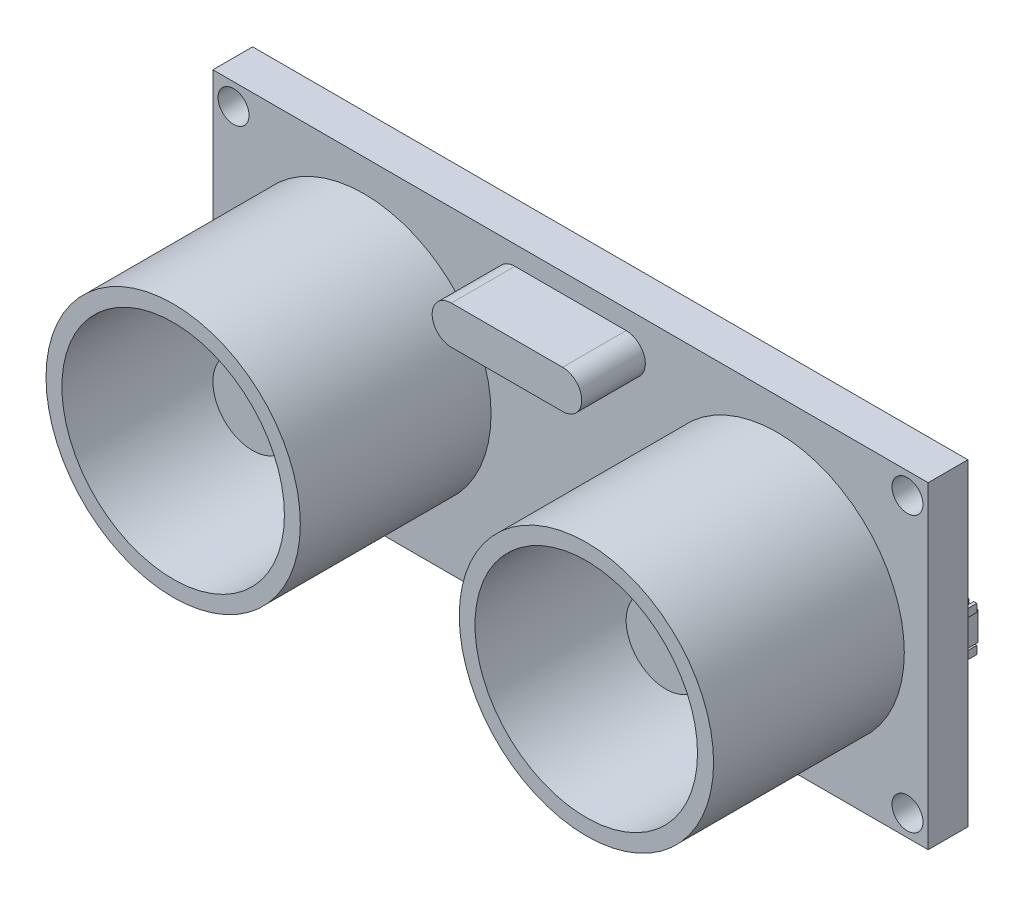
SolidWorks part; units mm, degrees
ref_plane "Front Plane" through (0, 0, 0) normal (0, 0, 1) x (1, 0, 0)
ref_plane "Top Plane" through (0, 0, 0) normal (0, 1, 0) x (1, 0, 0)
ref_plane "Right Plane" through (0, 0, 0) normal (1, 0, 0) x (0, 0, -1)
sketch "Sketch1" plane through (0, 0, 0) normal (0, 0, 1) x (1, 0, 0)
  line L1 (-22.5, 10) -> (22.5, 10)
  line L2 (-22.5, 10) -> (-22.5, -10)
  line L3 (-22.5, -10) -> (22.5, -10)
  line L4 (22.5, 10) -> (22.5, -10)
  line L5 (-22.5, 10) -> (22.5, -10) construction
  line L6 (-22.5, -10) -> (22.5, 10) construction
  point P0 (0, 0)
  dimension "D1" = 45
  dimension "D2" = 20
extrude "Boss-Extrude1" add sketch "Sketch1" along normal blind 2.5
sketch "Sketch2" plane through (0, 0, 2.5) normal (0, 0, 1) x (1, 0, 0)
  line L0 (22.5, 10) -> (-22.5, 10) construction
  line L2 (-22.5, 10) -> (-22.5, -10) construction
  line L3 (22.5, -10) -> (22.5, 10) construction
  circle A0 centre (-13, 0) radius 8
  circle A1 centre (13, 0) radius 8
  dimension "D1" = 16
  dimension "D2" = 16
  dimension "D3" = 9.5
  dimension "D4" = 9.5
  dimension "D5" = 10
extrude "Boss-Extrude2" add sketch "Sketch2" along normal blind 12
sketch "Sketch3" plane through (0, 0, 14.5) normal (0, 0, 1) x (1, 0, 0)
  circle A0 centre (-13, -0.01) radius 7
  circle A1 centre (12.99, 0) radius 7
  circle A2 centre (13, 0) radius 8 construction
  circle A3 centre (-13, 0) radius 8 construction
  dimension "D1" = 14
  dimension "D2" = 14
  dimension "D3" = 0.01
  dimension "D4" = 0.01
extrude "Cut-Extrude2" cut sketch "Sketch3" against normal blind 12 contours A1 | A0
sketch "Sketch5" plane through (0, 0, 2.5) normal (0, 0, 1) x (1, 0, 0)
  circle A0 centre (-13, 0) radius 4
  circle A1 centre (13, 0) radius 4
  dimension "D1" = 8
  dimension "D2" = 8
extrude "Boss-Extrude3" add sketch "Sketch5" along normal blind 5
sketch "Sketch6" plane through (0, 0, 7.5) normal (0, 0, 1) x (1, 0, 0)
  circle A0 centre (-13, 0) radius 2.5
  circle A1 centre (13, 0) radius 2.5
  dimension "D1" = 5
  dimension "D2" = 5
extrude "Boss-Extrude4" add sketch "Sketch6" along normal blind 2
sketch "Sketch7" plane through (0, 0, 2.5) normal (0, 0, 1) x (1, 0, 0)
  line L0 (-22.5, 10) -> (-22.5, -10) construction
  line L1 (22.5, 10) -> (-22.5, 10) construction
  line L2 (-22.5, -10) -> (22.5, -10) construction
  line L3 (22.5, -10) -> (22.5, 10) construction
  circle A0 centre (-21.2, 8.65) radius 0.975
  circle A1 centre (-21.2, -8.65) radius 0.975
  circle A2 centre (21.2, -8.65) radius 0.975
  circle A3 centre (21.2, 8.65) radius 0.975
  dimension "D1" = 1.3
  dimension "D9" = 1.95
  dimension "D10" = 1.95
  dimension "D11" = 1.95
  dimension "D12" = 1.95
  dimension "D2" = 1.35
  dimension "D3" = 1.3
  dimension "D4" = 1.35
  dimension "D5" = 1.35
  dimension "D6" = 1.3
  dimension "D7" = 1.3
  dimension "D8" = 1.35
  dimension "D13" = 17.3
  dimension "D14" = 42.4
  dimension "D15" = 42.4
  dimension "D16" = 17.3
extrude "Cut-Extrude4" cut sketch "Sketch7" against normal blind 12
sketch "Sketch8" plane through (0, 0, 2.5) normal (0, 0, 1) x (1, 0, 0)
  line L0 (-3.5, 7.585) -> (3.5, 7.585) construction
  line L1 (-3.5, 8.79) -> (3.5, 8.79)
  line L2 (-3.5, 6.38) -> (3.5, 6.38)
  line L3 (-22.5, 10) -> (-22.5, -10) construction
  line L4 (22.5, -10) -> (22.5, 10) construction
  line L5 (22.5, 10) -> (-22.5, 10) construction
  arc A0 (-3.5, 8.79) -> (-3.5, 6.38) centre (-3.5, 7.585) ccw
  arc A1 (3.5, 6.38) -> (3.5, 8.79) centre (3.5, 7.585) ccw
  point P2 (0, 7.585)
  dimension "D1" = 19
  dimension "D2" = 19
  dimension "D5" = 7
  dimension "D6" = 2.41
  dimension "D7" = 1.21
extrude "Boss-Extrude5" add sketch "Sketch8" along normal blind 4
sketch "Sketch9" plane through (0, 0, 0) normal (0, 0, -1) x (-1, 0, 0)
  line L1 (-22.136, 1.1575) -> (-17.0213, 1.1575)
  line L2 (-22.136, 1.1575) -> (-22.136, -0.6364)
  line L3 (-22.136, -0.6364) -> (-17.0213, -0.6364)
  line L4 (-17.0213, 1.1575) -> (-17.0213, -0.6364)
  line L5 (-22.136, 1.1575) -> (-17.0213, -0.6364) construction
  line L6 (-22.136, -0.6364) -> (-17.0213, 1.1575) construction
  point P0 (-19.5787, 0.2606)
extrude "Boss-Extrude6" add sketch "Sketch9" along normal blind 1
sketch "Sketch10" plane through (0, 0, 0) normal (0, 0, -1) x (-1, 0, 0)
  line L1 (-2.8938, 0.9646) -> (2.8938, 0.9646)
  line L2 (-2.8938, 0.9646) -> (-2.8938, -0.9646)
  line L3 (-2.8938, -0.9646) -> (2.8938, -0.9646)
  line L4 (2.8938, 0.9646) -> (2.8938, -0.9646)
  line L5 (-2.8938, 0.9646) -> (2.8938, -0.9646) construction
  line L6 (-2.8938, -0.9646) -> (2.8938, 0.9646) construction
  line L7 (19.4136, 2.315) -> (21.5357, 2.315)
  line L8 (19.4136, 2.315) -> (19.4136, -2.315)
  line L9 (19.4136, -2.315) -> (21.5357, -2.315)
  line L10 (21.5357, 2.315) -> (21.5357, -2.315)
  line L11 (19.4136, 2.315) -> (21.5357, -2.315) construction
  line L12 (19.4136, -2.315) -> (21.5357, 2.315) construction
  point P0 (0, 0)
  point P6 (20.4746, 0)
extrude "Boss-Extrude7" add sketch "Sketch10" along normal blind 1
sketch "Sketch12" plane through (0, 0, 0) normal (0, 0, -1) x (-1, 0, 0)
  circle A0 centre (-15.4898, 5.0275) radius 1
  circle A1 centre (-15.4898, -5.3069) radius 1
  circle A2 centre (13.7773, -5.3069) radius 1
  circle A3 centre (13.7773, 5.0275) radius 1
  dimension "D1" = 2
  dimension "D2" = 2
  dimension "D3" = 2
  dimension "D4" = 2
extrude "Boss-Extrude8" add sketch "Sketch12" along normal blind 0.5 draft 62
sketch "Sketch13" plane through (0, 0, 0) normal (0, 0, -1) x (-1, 0, 0)
  circle A0 centre (-3.3278, 7.138) radius 0.5
  circle A1 centre (3.9548, 7.138) radius 0.5
  dimension "D1" = 1
  dimension "D2" = 1
extrude "Boss-Extrude9" add sketch "Sketch13" along normal blind 0.5 draft 45
ref_plane "Plane1" through (0, 0, -0.8) normal (0, 0, 1) x (1, 0, 0)
sketch "Sketch15" plane through (0, 0, -0.8) normal (0, 0, 1) x (1, 0, 0)
  line L0 (17.0213, 1.1575) -> (22.136, 1.1575) construction
  line L1 (22.2579, 1.6575) -> (22.0579, 1.6575)
  line L2 (22.2579, 1.6575) -> (22.2579, 1.1575)
  line L3 (22.2579, 1.1575) -> (22.0579, 1.1575)
  line L4 (22.0579, 1.6575) -> (22.0579, 1.1575)
  line L5 (22.2579, 1.6575) -> (22.0579, 1.1575) construction
  line L6 (22.2579, 1.1575) -> (22.0579, 1.6575) construction
  line L7 (21.5579, 1.6575) -> (21.5579, 1.1575)
  line L8 (22.2579, -0.6364) -> (22.0579, -0.6364)
  line L9 (22.2579, -0.6364) -> (22.2579, -1.1364)
  line L10 (22.2579, -1.1364) -> (22.0579, -1.1364)
  line L11 (22.0579, -0.6364) -> (22.0579, -1.1364)
  line L12 (22.2579, -0.6364) -> (22.0579, -1.1364) construction
  line L13 (22.2579, -1.1364) -> (22.0579, -0.6364) construction
  line L14 (22.136, -0.6364) -> (17.0213, -0.6364) construction
  line L15 (21.7579, 1.6575) -> (21.5579, 1.6575)
  line L16 (21.7579, 1.6575) -> (21.7579, 1.1575)
  line L17 (21.7579, 1.1575) -> (21.5579, 1.1575)
  line L18 (21.7579, -0.6364) -> (21.5579, -0.6364)
  line L19 (21.5579, -0.6364) -> (21.5579, -1.1364)
  line L20 (21.7579, -1.1364) -> (21.5579, -1.1364)
  line L21 (21.7579, -0.6364) -> (21.7579, -1.1364)
  line L22 (21.0579, 1.6575) -> (21.0579, 1.1575)
  line L23 (21.2579, 1.6575) -> (21.0579, 1.6575)
  line L24 (21.2579, 1.6575) -> (21.2579, 1.1575)
  line L25 (21.2579, 1.1575) -> (21.0579, 1.1575)
  line L26 (21.2579, -0.6364) -> (21.0579, -0.6364)
  line L27 (21.0579, -0.6364) -> (21.0579, -1.1364)
  line L28 (21.2579, -1.1364) -> (21.0579, -1.1364)
  line L29 (21.2579, -0.6364) -> (21.2579, -1.1364)
  line L30 (20.5579, 1.6575) -> (20.5579, 1.1575)
  line L31 (20.7579, 1.6575) -> (20.5579, 1.6575)
  line L32 (20.7579, 1.6575) -> (20.7579, 1.1575)
  line L33 (20.7579, 1.1575) -> (20.5579, 1.1575)
  line L34 (20.7579, -0.6364) -> (20.5579, -0.6364)
  line L35 (20.5579, -0.6364) -> (20.5579, -1.1364)
  line L36 (20.7579, -1.1364) -> (20.5579, -1.1364)
  line L37 (20.7579, -0.6364) -> (20.7579, -1.1364)
  line L38 (20.0579, 1.6575) -> (20.0579, 1.1575)
  line L39 (20.2579, 1.6575) -> (20.0579, 1.6575)
  line L40 (20.2579, 1.6575) -> (20.2579, 1.1575)
  line L41 (20.2579, 1.1575) -> (20.0579, 1.1575)
  line L42 (20.2579, -0.6364) -> (20.0579, -0.6364)
  line L43 (20.0579, -0.6364) -> (20.0579, -1.1364)
  line L44 (20.2579, -1.1364) -> (20.0579, -1.1364)
  line L45 (20.2579, -0.6364) -> (20.2579, -1.1364)
  line L46 (19.5579, 1.6575) -> (19.5579, 1.1575)
  line L47 (19.7579, 1.6575) -> (19.5579, 1.6575)
  line L48 (19.7579, 1.6575) -> (19.7579, 1.1575)
  line L49 (19.7579, 1.1575) -> (19.5579, 1.1575)
  line L50 (19.7579, -0.6364) -> (19.5579, -0.6364)
  line L51 (19.5579, -0.6364) -> (19.5579, -1.1364)
  line L52 (19.7579, -1.1364) -> (19.5579, -1.1364)
  line L53 (19.7579, -0.6364) -> (19.7579, -1.1364)
  line L54 (19.0579, 1.6575) -> (19.0579, 1.1575)
  line L55 (19.2579, 1.6575) -> (19.0579, 1.6575)
  line L56 (19.2579, 1.6575) -> (19.2579, 1.1575)
  line L57 (19.2579, 1.1575) -> (19.0579, 1.1575)
  line L58 (19.2579, -0.6364) -> (19.0579, -0.6364)
  line L59 (19.0579, -0.6364) -> (19.0579, -1.1364)
  line L60 (19.2579, -1.1364) -> (19.0579, -1.1364)
  line L61 (19.2579, -0.6364) -> (19.2579, -1.1364)
  line L62 (18.5579, 1.6575) -> (18.5579, 1.1575)
  line L63 (18.7579, 1.6575) -> (18.5579, 1.6575)
  line L64 (18.7579, 1.6575) -> (18.7579, 1.1575)
  line L65 (18.7579, 1.1575) -> (18.5579, 1.1575)
  line L66 (18.7579, -0.6364) -> (18.5579, -0.6364)
  line L67 (18.5579, -0.6364) -> (18.5579, -1.1364)
  line L68 (18.7579, -1.1364) -> (18.5579, -1.1364)
  line L69 (18.7579, -0.6364) -> (18.7579, -1.1364)
  line L70 (18.0579, 1.6575) -> (18.0579, 1.1575)
  line L71 (18.2579, 1.6575) -> (18.0579, 1.6575)
  line L72 (18.2579, 1.6575) -> (18.2579, 1.1575)
  line L73 (18.2579, 1.1575) -> (18.0579, 1.1575)
  line L74 (18.2579, -0.6364) -> (18.0579, -0.6364)
  line L75 (18.0579, -0.6364) -> (18.0579, -1.1364)
  line L76 (18.2579, -1.1364) -> (18.0579, -1.1364)
  line L77 (18.2579, -0.6364) -> (18.2579, -1.1364)
  line L78 (17.5579, 1.6575) -> (17.5579, 1.1575)
  line L79 (17.7579, 1.6575) -> (17.5579, 1.6575)
  line L80 (17.7579, 1.6575) -> (17.7579, 1.1575)
  line L81 (17.7579, 1.1575) -> (17.5579, 1.1575)
  line L82 (17.7579, -0.6364) -> (17.5579, -0.6364)
  line L83 (17.5579, -0.6364) -> (17.5579, -1.1364)
  line L84 (17.7579, -1.1364) -> (17.5579, -1.1364)
  line L85 (17.7579, -0.6364) -> (17.7579, -1.1364)
  line L86 (22.0579, 1.6575) -> (21.5579, 1.6575) construction
  point P0 (22.1579, 1.4075)
  point P7 (22.1579, -0.8864)
  dimension "D1" = 0.5
  dimension "D2" = 0.2
  dimension "D3" = 0.2
  dimension "D4" = 0.5
  dimension "D5" = 10
  dimension "D6" = 0.5
extrude "Boss-Extrude10" add sketch "Sketch15" along normal up to surface (0.8 mm away) up to face at (-3.4548, 7.138, 0)
sketch "Sketch16" plane through (0, 0, -0.8) normal (0, 0, 1) x (1, 0, 0)
  line L0 (-2.8938, 0.9646) -> (2.8938, 0.9646) construction
  line L1 (2.7664, 1.4646) -> (2.5664, 1.4646)
  line L2 (2.7664, 1.4646) -> (2.7664, 0.9646)
  line L3 (2.7664, 0.9646) -> (2.5664, 0.9646)
  line L4 (2.5664, 1.4646) -> (2.5664, 0.9646)
  line L5 (2.7664, 1.4646) -> (2.5664, 0.9646) construction
  line L6 (2.7664, 0.9646) -> (2.5664, 1.4646) construction
  line L7 (2.2664, 1.4646) -> (2.0664, 1.4646)
  line L8 (2.7664, -0.9646) -> (2.5664, -0.9646)
  line L9 (2.7664, -0.9646) -> (2.7664, -1.4646)
  line L10 (2.7664, -1.4646) -> (2.5664, -1.4646)
  line L11 (2.5664, -0.9646) -> (2.5664, -1.4646)
  line L12 (2.7664, -0.9646) -> (2.5664, -1.4646) construction
  line L13 (2.7664, -1.4646) -> (2.5664, -0.9646) construction
  line L14 (-2.8938, 0.9646) -> (2.8938, 0.9646) construction
  line L15 (2.8938, -0.9646) -> (-2.8938, -0.9646) construction
  line L16 (2.0664, 1.4646) -> (2.0664, 0.9646)
  line L17 (2.2664, 0.9646) -> (2.0664, 0.9646)
  line L18 (2.2664, 1.4646) -> (2.2664, 0.9646)
  line L19 (2.2664, -1.4646) -> (2.0664, -1.4646)
  line L20 (2.2664, -0.9646) -> (2.2664, -1.4646)
  line L21 (2.2664, -0.9646) -> (2.0664, -0.9646)
  line L22 (2.0664, -0.9646) -> (2.0664, -1.4646)
  line L23 (1.7664, 1.4646) -> (1.5664, 1.4646)
  line L24 (1.5664, 1.4646) -> (1.5664, 0.9646)
  line L25 (1.7664, 0.9646) -> (1.5664, 0.9646)
  line L26 (1.7664, 1.4646) -> (1.7664, 0.9646)
  line L27 (1.7664, -1.4646) -> (1.5664, -1.4646)
  line L28 (1.7664, -0.9646) -> (1.7664, -1.4646)
  line L29 (1.7664, -0.9646) -> (1.5664, -0.9646)
  line L30 (1.5664, -0.9646) -> (1.5664, -1.4646)
  line L31 (1.2664, 1.4646) -> (1.0664, 1.4646)
  line L32 (1.0664, 1.4646) -> (1.0664, 0.9646)
  line L33 (1.2664, 0.9646) -> (1.0664, 0.9646)
  line L34 (1.2664, 1.4646) -> (1.2664, 0.9646)
  line L35 (1.2664, -1.4646) -> (1.0664, -1.4646)
  line L36 (1.2664, -0.9646) -> (1.2664, -1.4646)
  line L37 (1.2664, -0.9646) -> (1.0664, -0.9646)
  line L38 (1.0664, -0.9646) -> (1.0664, -1.4646)
  line L39 (0.7664, 1.4646) -> (0.5664, 1.4646)
  line L40 (0.5664, 1.4646) -> (0.5664, 0.9646)
  line L41 (0.7664, 0.9646) -> (0.5664, 0.9646)
  line L42 (0.7664, 1.4646) -> (0.7664, 0.9646)
  line L43 (0.7664, -1.4646) -> (0.5664, -1.4646)
  line L44 (0.7664, -0.9646) -> (0.7664, -1.4646)
  line L45 (0.7664, -0.9646) -> (0.5664, -0.9646)
  line L46 (0.5664, -0.9646) -> (0.5664, -1.4646)
  line L47 (0.2664, 1.4646) -> (0.0664, 1.4646)
  line L48 (0.0664, 1.4646) -> (0.0664, 0.9646)
  line L49 (0.2664, 0.9646) -> (0.0664, 0.9646)
  line L50 (0.2664, 1.4646) -> (0.2664, 0.9646)
  line L51 (0.2664, -1.4646) -> (0.0664, -1.4646)
  line L52 (0.2664, -0.9646) -> (0.2664, -1.4646)
  line L53 (0.2664, -0.9646) -> (0.0664, -0.9646)
  line L54 (0.0664, -0.9646) -> (0.0664, -1.4646)
  line L55 (-0.2336, 1.4646) -> (-0.4336, 1.4646)
  line L56 (-0.4336, 1.4646) -> (-0.4336, 0.9646)
  line L57 (-0.2336, 0.9646) -> (-0.4336, 0.9646)
  line L58 (-0.2336, 1.4646) -> (-0.2336, 0.9646)
  line L59 (-0.2336, -1.4646) -> (-0.4336, -1.4646)
  line L60 (-0.2336, -0.9646) -> (-0.2336, -1.4646)
  line L61 (-0.2336, -0.9646) -> (-0.4336, -0.9646)
  line L62 (-0.4336, -0.9646) -> (-0.4336, -1.4646)
  line L63 (-0.7336, 1.4646) -> (-0.9336, 1.4646)
  line L64 (-0.9336, 1.4646) -> (-0.9336, 0.9646)
  line L65 (-0.7336, 0.9646) -> (-0.9336, 0.9646)
  line L66 (-0.7336, 1.4646) -> (-0.7336, 0.9646)
  line L67 (-0.7336, -1.4646) -> (-0.9336, -1.4646)
  line L68 (-0.7336, -0.9646) -> (-0.7336, -1.4646)
  line L69 (-0.7336, -0.9646) -> (-0.9336, -0.9646)
  line L70 (-0.9336, -0.9646) -> (-0.9336, -1.4646)
  line L71 (-1.2336, 1.4646) -> (-1.4336, 1.4646)
  line L72 (-1.4336, 1.4646) -> (-1.4336, 0.9646)
  line L73 (-1.2336, 0.9646) -> (-1.4336, 0.9646)
  line L74 (-1.2336, 1.4646) -> (-1.2336, 0.9646)
  line L75 (-1.2336, -1.4646) -> (-1.4336, -1.4646)
  line L76 (-1.2336, -0.9646) -> (-1.2336, -1.4646)
  line L77 (-1.2336, -0.9646) -> (-1.4336, -0.9646)
  line L78 (-1.4336, -0.9646) -> (-1.4336, -1.4646)
  line L79 (-1.7336, 1.4646) -> (-1.9336, 1.4646)
  line L80 (-1.9336, 1.4646) -> (-1.9336, 0.9646)
  line L81 (-1.7336, 0.9646) -> (-1.9336, 0.9646)
  line L82 (-1.7336, 1.4646) -> (-1.7336, 0.9646)
  line L83 (-1.7336, -1.4646) -> (-1.9336, -1.4646)
  line L84 (-1.7336, -0.9646) -> (-1.7336, -1.4646)
  line L85 (-1.7336, -0.9646) -> (-1.9336, -0.9646)
  line L86 (-1.9336, -0.9646) -> (-1.9336, -1.4646)
  line L87 (-2.2336, 1.4646) -> (-2.4336, 1.4646)
  line L88 (-2.4336, 1.4646) -> (-2.4336, 0.9646)
  line L89 (-2.2336, 0.9646) -> (-2.4336, 0.9646)
  line L90 (-2.2336, 1.4646) -> (-2.2336, 0.9646)
  line L91 (-2.2336, -1.4646) -> (-2.4336, -1.4646)
  line L92 (-2.2336, -0.9646) -> (-2.2336, -1.4646)
  line L93 (-2.2336, -0.9646) -> (-2.4336, -0.9646)
  line L94 (-2.4336, -0.9646) -> (-2.4336, -1.4646)
  line L95 (2.7664, 1.4646) -> (2.2664, 1.4646) construction
  point P0 (2.6664, 1.2146)
  point P7 (2.6664, -1.2146)
  dimension "D1" = 0.5
  dimension "D2" = 0.2
  dimension "D3" = 0.5
  dimension "D4" = 0.2
  dimension "D6" = 0.5
  dimension "D5" = 11
extrude "Boss-Extrude11" add sketch "Sketch16" along normal up to surface (0.8 mm away) up to face at (-3.4548, 7.138, 0)
sketch "Sketch17" plane through (0, 0, -0.8) normal (0, 0, 1) x (1, 0, 0)
  line L0 (-19.4136, 2.1119) -> (-21.5357, 2.1119) construction
  line L1 (-21.5357, 2.1119) -> (-22.079, 2.1119)
  line L2 (-21.5357, 2.1119) -> (-21.5357, 1.9119)
  line L3 (-21.5357, 1.9119) -> (-22.079, 1.9119)
  line L4 (-22.079, 2.1119) -> (-22.079, 1.9119)
  line L5 (-21.5357, 2.1119) -> (-22.079, 1.9119) construction
  line L6 (-21.5357, 1.9119) -> (-22.079, 2.1119) construction
  line L7 (-18.9136, 2.1119) -> (-19.4136, 2.1119)
  line L8 (-18.9136, 2.1119) -> (-18.9136, 1.9119)
  line L9 (-18.9136, 1.9119) -> (-19.4136, 1.9119)
  line L10 (-19.4136, 2.1119) -> (-19.4136, 1.9119)
  line L11 (-18.9136, 2.1119) -> (-19.4136, 1.9119) construction
  line L12 (-18.9136, 1.9119) -> (-19.4136, 2.1119) construction
  line L13 (-19.4136, 2.315) -> (-19.4136, -2.315) construction
  line L14 (-21.5357, -2.315) -> (-21.5357, 2.315) construction
  line L15 (-18.9136, 1.6119) -> (-19.4136, 1.6119)
  line L16 (-18.9136, 1.6119) -> (-18.9136, 1.4119)
  line L17 (-18.9136, 1.4119) -> (-19.4136, 1.4119)
  line L18 (-19.4136, 1.6119) -> (-19.4136, 1.4119)
  line L19 (-21.5357, 1.6119) -> (-22.079, 1.6119)
  line L20 (-21.5357, 1.6119) -> (-21.5357, 1.4119)
  line L21 (-21.5357, 1.4119) -> (-22.079, 1.4119)
  line L22 (-22.079, 1.6119) -> (-22.079, 1.4119)
  line L23 (-18.9136, 1.1119) -> (-19.4136, 1.1119)
  line L24 (-18.9136, 1.1119) -> (-18.9136, 0.9119)
  line L25 (-18.9136, 0.9119) -> (-19.4136, 0.9119)
  line L26 (-19.4136, 1.1119) -> (-19.4136, 0.9119)
  line L27 (-21.5357, 1.1119) -> (-22.079, 1.1119)
  line L28 (-21.5357, 1.1119) -> (-21.5357, 0.9119)
  line L29 (-21.5357, 0.9119) -> (-22.079, 0.9119)
  line L30 (-22.079, 1.1119) -> (-22.079, 0.9119)
  line L31 (-18.9136, 0.6119) -> (-19.4136, 0.6119)
  line L32 (-18.9136, 0.6119) -> (-18.9136, 0.4119)
  line L33 (-18.9136, 0.4119) -> (-19.4136, 0.4119)
  line L34 (-19.4136, 0.6119) -> (-19.4136, 0.4119)
  line L35 (-21.5357, 0.6119) -> (-22.079, 0.6119)
  line L36 (-21.5357, 0.6119) -> (-21.5357, 0.4119)
  line L37 (-21.5357, 0.4119) -> (-22.079, 0.4119)
  line L38 (-22.079, 0.6119) -> (-22.079, 0.4119)
  line L39 (-18.9136, 0.1119) -> (-19.4136, 0.1119)
  line L40 (-18.9136, 0.1119) -> (-18.9136, -0.0881)
  line L41 (-18.9136, -0.0881) -> (-19.4136, -0.0881)
  line L42 (-19.4136, 0.1119) -> (-19.4136, -0.0881)
  line L43 (-21.5357, 0.1119) -> (-22.079, 0.1119)
  line L44 (-21.5357, 0.1119) -> (-21.5357, -0.0881)
  line L45 (-21.5357, -0.0881) -> (-22.079, -0.0881)
  line L46 (-22.079, 0.1119) -> (-22.079, -0.0881)
  line L47 (-18.9136, -0.3881) -> (-19.4136, -0.3881)
  line L48 (-18.9136, -0.3881) -> (-18.9136, -0.5881)
  line L49 (-18.9136, -0.5881) -> (-19.4136, -0.5881)
  line L50 (-19.4136, -0.3881) -> (-19.4136, -0.5881)
  line L51 (-21.5357, -0.3881) -> (-22.079, -0.3881)
  line L52 (-21.5357, -0.3881) -> (-21.5357, -0.5881)
  line L53 (-21.5357, -0.5881) -> (-22.079, -0.5881)
  line L54 (-22.079, -0.3881) -> (-22.079, -0.5881)
  line L55 (-18.9136, -0.8881) -> (-19.4136, -0.8881)
  line L56 (-18.9136, -0.8881) -> (-18.9136, -1.0881)
  line L57 (-18.9136, -1.0881) -> (-19.4136, -1.0881)
  line L58 (-19.4136, -0.8881) -> (-19.4136, -1.0881)
  line L59 (-21.5357, -0.8881) -> (-22.079, -0.8881)
  line L60 (-21.5357, -0.8881) -> (-21.5357, -1.0881)
  line L61 (-21.5357, -1.0881) -> (-22.079, -1.0881)
  line L62 (-22.079, -0.8881) -> (-22.079, -1.0881)
  line L63 (-18.9136, -1.3881) -> (-19.4136, -1.3881)
  line L64 (-18.9136, -1.3881) -> (-18.9136, -1.5881)
  line L65 (-18.9136, -1.5881) -> (-19.4136, -1.5881)
  line L66 (-19.4136, -1.3881) -> (-19.4136, -1.5881)
  line L67 (-21.5357, -1.3881) -> (-22.079, -1.3881)
  line L68 (-21.5357, -1.3881) -> (-21.5357, -1.5881)
  line L69 (-21.5357, -1.5881) -> (-22.079, -1.5881)
  line L70 (-22.079, -1.3881) -> (-22.079, -1.5881)
  line L71 (-18.9136, -1.8881) -> (-19.4136, -1.8881)
  line L72 (-18.9136, -1.8881) -> (-18.9136, -2.0881)
  line L73 (-18.9136, -2.0881) -> (-19.4136, -2.0881)
  line L74 (-19.4136, -1.8881) -> (-19.4136, -2.0881)
  line L75 (-21.5357, -1.8881) -> (-22.079, -1.8881)
  line L76 (-21.5357, -1.8881) -> (-21.5357, -2.0881)
  line L77 (-21.5357, -2.0881) -> (-22.079, -2.0881)
  line L78 (-22.079, -1.8881) -> (-22.079, -2.0881)
  point P0 (-21.8074, 2.0119)
  point P5 (-19.1636, 2.0119)
  dimension "D1" = 0.2
  dimension "D2" = 0.5
  dimension "D3" = 0.5433
  dimension "D4" = 0.2
  dimension "D5" = 9
extrude "Boss-Extrude12" add sketch "Sketch17" along normal up to surface (0.8 mm away) up to face at (-3.4548, 7.138, 0)
sketch "Sketch18" plane through (0, 0, 0) normal (0, 0, -1) x (-1, 0, 0)
  line L1 (-4.5, -7.199) -> (4.5, -7.199)
  line L2 (-4.5, -7.199) -> (-4.5, -9.199)
  line L3 (-4.5, -9.199) -> (4.5, -9.199)
  line L4 (4.5, -7.199) -> (4.5, -9.199)
  line L5 (-4.5, -7.199) -> (4.5, -9.199) construction
  line L6 (-4.5, -9.199) -> (4.5, -7.199) construction
  line L8 (-22.5, -10) -> (-22.5, 10) construction
  line L9 (22.5, 10) -> (22.5, -10) construction
  point P0 (0, -8.199)
  dimension "D1" = 18
  dimension "D2" = 18
  dimension "D3" = 2
extrude "Boss-Extrude14" add sketch "Sketch18" along normal blind 3 contours L3 L4 L1 L2
sketch "Sketch19" plane through (0, 0, -3) normal (0, 0, -1) x (-1, 0, 0)
  line L1 (-3.858, -7.956) -> (-3.358, -7.956)
  line L2 (-3.858, -7.956) -> (-3.858, -8.456)
  line L3 (-3.858, -8.456) -> (-3.358, -8.456)
  line L4 (-3.358, -7.956) -> (-3.358, -8.456)
  line L5 (-3.858, -7.956) -> (-3.358, -8.456) construction
  line L6 (-3.858, -8.456) -> (-3.358, -7.956) construction
  line L7 (-4.5, -9.199) -> (4.5, -9.199) construction
  line L8 (-4.5, -7.199) -> (4.5, -7.199) construction
  line L9 (-0.858, -7.956) -> (-0.858, -8.456)
  line L10 (-1.358, -7.956) -> (-1.358, -8.456)
  line L11 (-1.358, -7.956) -> (-0.858, -7.956)
  line L12 (-1.358, -8.456) -> (-0.858, -8.456)
  line L13 (1.642, -7.956) -> (1.642, -8.456)
  line L14 (1.142, -7.956) -> (1.142, -8.456)
  line L15 (1.142, -7.956) -> (1.642, -7.956)
  line L16 (1.142, -8.456) -> (1.642, -8.456)
  line L17 (4.142, -7.956) -> (4.142, -8.456)
  line L18 (3.642, -7.956) -> (3.642, -8.456)
  line L19 (3.642, -7.956) -> (4.142, -7.956)
  line L20 (3.642, -8.456) -> (4.142, -8.456)
  point P0 (-3.608, -8.206)
  dimension "D1" = 0.5
  dimension "D2" = 0.5
  dimension "D3" = 0.993
  dimension "D4" = 1.007
  dimension "D5" = 4
extrude "Boss-Extrude15" add sketch "Sketch19" along normal blind 1
sketch "Sketch20" plane through (0, -8.456, 0) normal (0, -1, 0) x (1, 0, 0)
  line L0 (3.858, -4) -> (3.858, -3) construction
  line L1 (3.358, -3.4876) -> (3.858, -3.4876)
  line L2 (3.358, -3.4876) -> (3.358, -4)
  line L3 (3.358, -4) -> (3.858, -4)
  line L4 (3.858, -3.4876) -> (3.858, -4)
  line L5 (3.358, -3.4876) -> (3.858, -4) construction
  line L6 (3.358, -4) -> (3.858, -3.4876) construction
  line L7 (3.858, -4) -> (3.358, -4) construction
  line L8 (3.358, -4) -> (3.358, -3) construction
  line L9 (0.858, -3.4876) -> (1.358, -3.4876)
  line L10 (1.358, -3.4876) -> (1.358, -4)
  line L11 (0.858, -4) -> (1.358, -4)
  line L12 (0.858, -3.4876) -> (0.858, -4)
  line L13 (-1.642, -3.4876) -> (-1.142, -3.4876)
  line L14 (-1.142, -3.4876) -> (-1.142, -4)
  line L15 (-1.642, -4) -> (-1.142, -4)
  line L16 (-1.642, -3.4876) -> (-1.642, -4)
  line L17 (-4.142, -3.4876) -> (-3.642, -3.4876)
  line L18 (-3.642, -3.4876) -> (-3.642, -4)
  line L19 (-4.142, -4) -> (-3.642, -4)
  line L20 (-4.142, -3.4876) -> (-4.142, -4)
  point P0 (3.608, -3.7438)
  dimension "D1" = 4
extrude "Boss-Extrude16" add sketch "Sketch20" along normal blind 7
